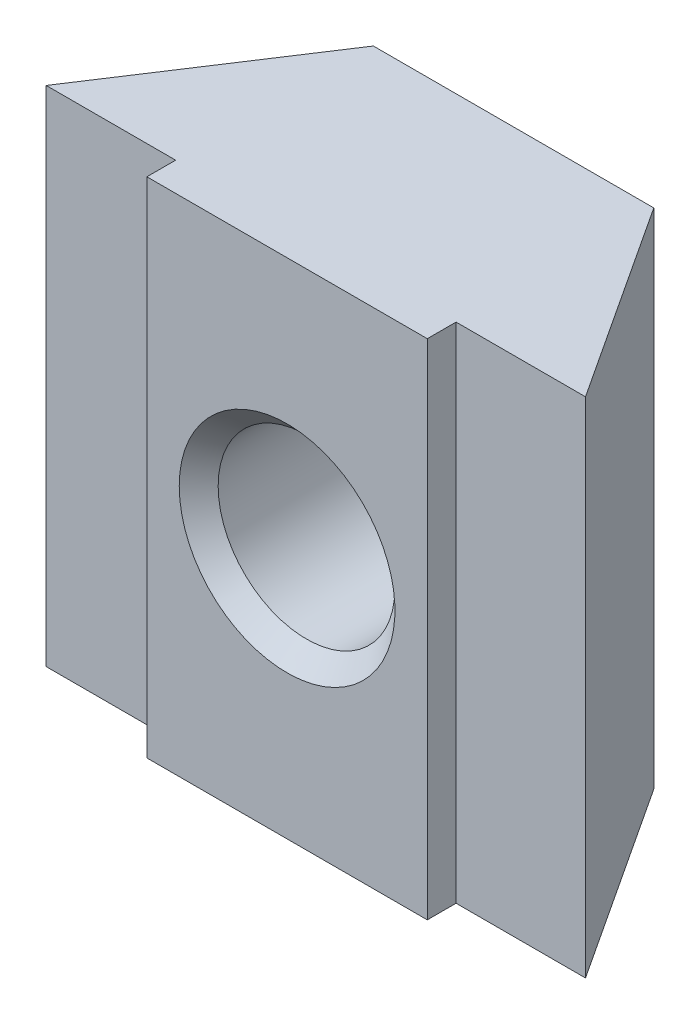
SolidWorks part; units mm, degrees
ref_plane "Piano frontale" through (0, 0, 0) normal (0, 0, 1) x (1, 0, 0)
ref_plane "Piano superiore" through (0, 0, 0) normal (0, 1, 0) x (1, 0, 0)
ref_plane "Piano destro" through (0, 0, 0) normal (1, 0, 0) x (0, 0, -1)
ref_plane "Plane1" through (0, 28.5, 0) normal (0, 1, 0) x (1, 0, 0)
sketch "Sketch1" plane through (0, 28.5, 0) normal (0, 1, 0) x (1, 0, 0)
  line L0 (11.6, 15.6) -> (8, 10.1)
  line L1 (8, 10.1) -> (23, 10.1)
  line L2 (23, 10.1) -> (19.4, 15.6)
  line L3 (19.4, 15.6) -> (11.6, 15.6)
extrude "Extrude1" add sketch "Sketch1" against normal blind 14
sketch "Sketch2" plane through (0, 0, -10.1) normal (0, 0, 1) x (1, 0, 0)
  line L0 (19.4, 14.5) -> (11.6, 14.5)
  line L1 (11.6, 14.5) -> (11.6, 28.5)
  line L2 (11.6, 28.5) -> (19.4, 28.5)
  line L3 (19.4, 28.5) -> (19.4, 14.5)
extrude "Extrude2" add sketch "Sketch2" along normal blind 0.8
hole_wizard "HoleWzd1" positions "Sketch4" profile "Sketch3" legacy
sketch "Sketch4" plane through (0, 0, -9.3) normal (0, 0, 1) x (1, 0, 0)
  point P0 (15.5, 21.5)
sketch "Sketch3" plane through (15.5, 21.5, -9.3) normal (1, 0, 0) x (0, -1, 0)
  line L0 (0, 0) -> (0, 6.3)
  line L1 (0, 6.3) -> (2.4585, 6.3)
  line L2 (2.4585, 6.3) -> (2.4585, 0)
  line L3 (2.4585, 0) -> (0, 0)
  line L4 (0, 110) -> (0, -10) construction
  dimension "Diameter" = 4.917
  dimension "Depth" = 6.3
chamfer "Chamfer1" distance 0.5415 angle 45 2 edges at (17.9585, 21.5, -15.6) (17.9585, 21.5, -9.3)
